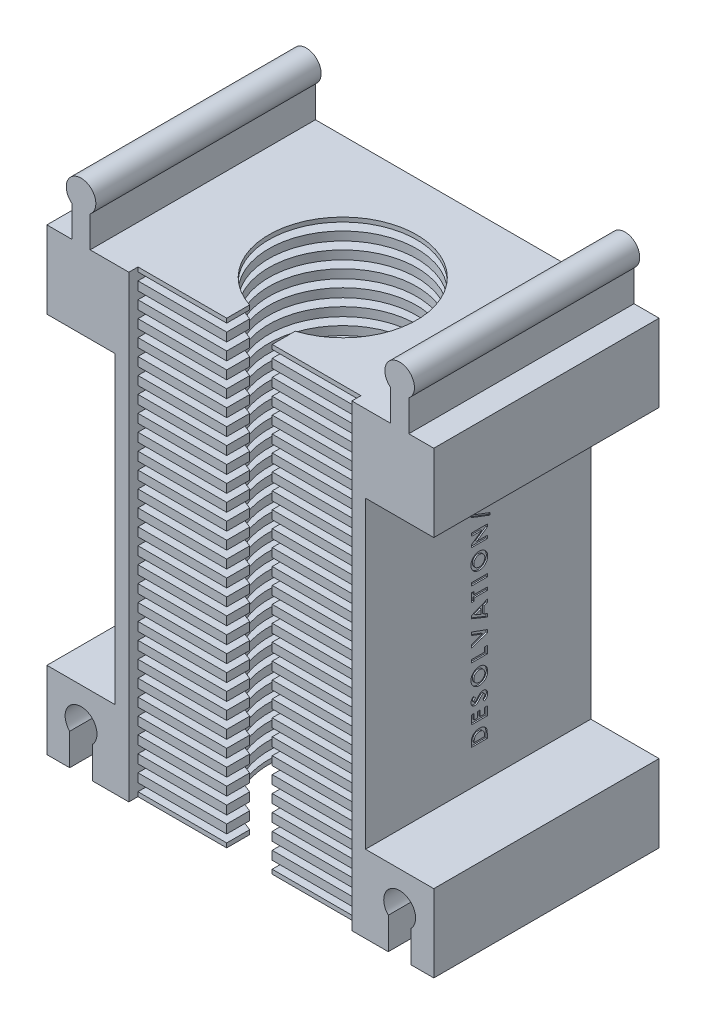
SolidWorks part; units mm, degrees
ref_plane "Plan de face" through (0, 0, 0) normal (0, 0, 1) x (1, 0, 0)
ref_plane "Plan de dessus" through (0, 0, 0) normal (0, 1, 0) x (1, 0, 0)
ref_plane "Plan de droite" through (0, 0, 0) normal (1, 0, 0) x (0, 0, -1)
sketch "Esquisse1" plane through (0, 0, 0) normal (0, 0, 1) x (1, 0, 0)
  line L1 (-20.1477, 24.3067) -> (34.8523, 24.3067)
  line L2 (-20.1477, 24.3067) -> (-20.1477, -82.2433)
  line L3 (-20.1477, -82.2433) -> (34.8523, -82.2433)
  line L4 (34.8523, 24.3067) -> (34.8523, -82.2433)
  dimension "D1" = 55
  dimension "D2" = 106.55
extrude "Boss.-Extru.2" add sketch "Esquisse1" along normal blind 49.5
sketch "Esquisse6" plane through (0, 0, 49.5) normal (0, 0, 1) x (1, 0, 0)
  line L0 (-20.1477, -82.2433) -> (34.8523, -82.2433) construction
  line L1 (-17.1477, 19.5067) -> (31.8523, 19.5067)
  line L2 (-17.1477, 19.5067) -> (-17.1477, -82.2433)
  line L3 (-17.1477, -82.2433) -> (31.8523, -82.2433)
  line L4 (31.8523, 19.5067) -> (31.8523, -82.2433)
  line L5 (-20.1477, 24.3067) -> (-20.1477, -82.2433) construction
  dimension "D1" = 49
  dimension "D2" = 3
  dimension "D3" = 101.75
extrude "Enlèv. mat.-Extru.2" cut sketch "Esquisse6" against normal blind 47
sketch "Esquisse7" plane through (0, 0, 2.5) normal (0, 0, 1) x (1, 0, 0)
  line L0 (31.8523, -82.2433) -> (31.8523, 19.5067) construction
  line L1 (-17.1477, -82.2433) -> (31.8523, -82.2433)
  line L2 (-17.1477, -82.2433) -> (-17.1477, -80.3433)
  line L3 (-17.1477, -80.3433) -> (31.8523, -80.3433)
  line L4 (31.8523, -82.2433) -> (31.8523, -80.3433)
  line L5 (-17.1477, -78.6433) -> (-17.1477, -76.7433)
  line L6 (-17.1477, -78.6433) -> (31.8523, -78.6433)
  line L7 (31.8523, -78.6433) -> (31.8523, -76.7433)
  line L8 (-17.1477, -76.7433) -> (31.8523, -76.7433)
  line L9 (-17.1477, -75.0433) -> (-17.1477, -73.1433)
  line L10 (-17.1477, -75.0433) -> (31.8523, -75.0433)
  line L11 (31.8523, -75.0433) -> (31.8523, -73.1433)
  line L12 (-17.1477, -73.1433) -> (31.8523, -73.1433)
  line L13 (-17.1477, -71.4433) -> (-17.1477, -69.5433)
  line L14 (-17.1477, -71.4433) -> (31.8523, -71.4433)
  line L15 (31.8523, -71.4433) -> (31.8523, -69.5433)
  line L16 (-17.1477, -69.5433) -> (31.8523, -69.5433)
  line L17 (-17.1477, -67.8433) -> (-17.1477, -65.9433)
  line L18 (-17.1477, -67.8433) -> (31.8523, -67.8433)
  line L19 (31.8523, -67.8433) -> (31.8523, -65.9433)
  line L20 (-17.1477, -65.9433) -> (31.8523, -65.9433)
  line L21 (-17.1477, -64.2433) -> (-17.1477, -62.3433)
  line L22 (-17.1477, -64.2433) -> (31.8523, -64.2433)
  line L23 (31.8523, -64.2433) -> (31.8523, -62.3433)
  line L24 (-17.1477, -62.3433) -> (31.8523, -62.3433)
  line L25 (-17.1477, -60.6433) -> (-17.1477, -58.7433)
  line L26 (-17.1477, -60.6433) -> (31.8523, -60.6433)
  line L27 (31.8523, -60.6433) -> (31.8523, -58.7433)
  line L28 (-17.1477, -58.7433) -> (31.8523, -58.7433)
  line L29 (-17.1477, -57.0433) -> (-17.1477, -55.1433)
  line L30 (-17.1477, -57.0433) -> (31.8523, -57.0433)
  line L31 (31.8523, -57.0433) -> (31.8523, -55.1433)
  line L32 (-17.1477, -55.1433) -> (31.8523, -55.1433)
  line L33 (-17.1477, -53.4433) -> (-17.1477, -51.5433)
  line L34 (-17.1477, -53.4433) -> (31.8523, -53.4433)
  line L35 (31.8523, -53.4433) -> (31.8523, -51.5433)
  line L36 (-17.1477, -51.5433) -> (31.8523, -51.5433)
  line L37 (-17.1477, -49.8433) -> (-17.1477, -47.9433)
  line L38 (-17.1477, -49.8433) -> (31.8523, -49.8433)
  line L39 (31.8523, -49.8433) -> (31.8523, -47.9433)
  line L40 (-17.1477, -47.9433) -> (31.8523, -47.9433)
  line L41 (-17.1477, -46.2433) -> (-17.1477, -44.3433)
  line L42 (-17.1477, -46.2433) -> (31.8523, -46.2433)
  line L43 (31.8523, -46.2433) -> (31.8523, -44.3433)
  line L44 (-17.1477, -44.3433) -> (31.8523, -44.3433)
  line L45 (-17.1477, -42.6433) -> (-17.1477, -40.7433)
  line L46 (-17.1477, -42.6433) -> (31.8523, -42.6433)
  line L47 (31.8523, -42.6433) -> (31.8523, -40.7433)
  line L48 (-17.1477, -40.7433) -> (31.8523, -40.7433)
  line L49 (-17.1477, -39.0433) -> (-17.1477, -37.1433)
  line L50 (-17.1477, -39.0433) -> (31.8523, -39.0433)
  line L51 (31.8523, -39.0433) -> (31.8523, -37.1433)
  line L52 (-17.1477, -37.1433) -> (31.8523, -37.1433)
  line L53 (-17.1477, -35.4433) -> (-17.1477, -33.5433)
  line L54 (-17.1477, -35.4433) -> (31.8523, -35.4433)
  line L55 (31.8523, -35.4433) -> (31.8523, -33.5433)
  line L56 (-17.1477, -33.5433) -> (31.8523, -33.5433)
  line L57 (-17.1477, -31.8433) -> (-17.1477, -29.9433)
  line L58 (-17.1477, -31.8433) -> (31.8523, -31.8433)
  line L59 (31.8523, -31.8433) -> (31.8523, -29.9433)
  line L60 (-17.1477, -29.9433) -> (31.8523, -29.9433)
  line L61 (-17.1477, -28.2433) -> (-17.1477, -26.3433)
  line L62 (-17.1477, -28.2433) -> (31.8523, -28.2433)
  line L63 (31.8523, -28.2433) -> (31.8523, -26.3433)
  line L64 (-17.1477, -26.3433) -> (31.8523, -26.3433)
  line L65 (-17.1477, -24.6433) -> (-17.1477, -22.7433)
  line L66 (-17.1477, -24.6433) -> (31.8523, -24.6433)
  line L67 (31.8523, -24.6433) -> (31.8523, -22.7433)
  line L68 (-17.1477, -22.7433) -> (31.8523, -22.7433)
  line L69 (-17.1477, -21.0433) -> (-17.1477, -19.1433)
  line L70 (-17.1477, -21.0433) -> (31.8523, -21.0433)
  line L71 (31.8523, -21.0433) -> (31.8523, -19.1433)
  line L72 (-17.1477, -19.1433) -> (31.8523, -19.1433)
  line L73 (-17.1477, -17.4433) -> (-17.1477, -15.5433)
  line L74 (-17.1477, -17.4433) -> (31.8523, -17.4433)
  line L75 (31.8523, -17.4433) -> (31.8523, -15.5433)
  line L76 (-17.1477, -15.5433) -> (31.8523, -15.5433)
  line L77 (-17.1477, -13.8433) -> (-17.1477, -11.9433)
  line L78 (-17.1477, -13.8433) -> (31.8523, -13.8433)
  line L79 (31.8523, -13.8433) -> (31.8523, -11.9433)
  line L80 (-17.1477, -11.9433) -> (31.8523, -11.9433)
  line L81 (-17.1477, -10.2433) -> (-17.1477, -8.3433)
  line L82 (-17.1477, -10.2433) -> (31.8523, -10.2433)
  line L83 (31.8523, -10.2433) -> (31.8523, -8.3433)
  line L84 (-17.1477, -8.3433) -> (31.8523, -8.3433)
  line L85 (-17.1477, -6.6433) -> (-17.1477, -4.7433)
  line L86 (-17.1477, -6.6433) -> (31.8523, -6.6433)
  line L87 (31.8523, -6.6433) -> (31.8523, -4.7433)
  line L88 (-17.1477, -4.7433) -> (31.8523, -4.7433)
  line L89 (-17.1477, -3.0433) -> (-17.1477, -1.1433)
  line L90 (-17.1477, -3.0433) -> (31.8523, -3.0433)
  line L91 (31.8523, -3.0433) -> (31.8523, -1.1433)
  line L92 (-17.1477, -1.1433) -> (31.8523, -1.1433)
  line L93 (-17.1477, 0.5567) -> (-17.1477, 2.4567)
  line L94 (-17.1477, 0.5567) -> (31.8523, 0.5567)
  line L95 (31.8523, 0.5567) -> (31.8523, 2.4567)
  line L96 (-17.1477, 2.4567) -> (31.8523, 2.4567)
  line L97 (-17.1477, 4.1567) -> (-17.1477, 6.0567)
  line L98 (-17.1477, 4.1567) -> (31.8523, 4.1567)
  line L99 (31.8523, 4.1567) -> (31.8523, 6.0567)
  line L100 (-17.1477, 6.0567) -> (31.8523, 6.0567)
  line L101 (-17.1477, 7.7567) -> (-17.1477, 9.6567)
  line L102 (-17.1477, 7.7567) -> (31.8523, 7.7567)
  line L103 (31.8523, 7.7567) -> (31.8523, 9.6567)
  line L104 (-17.1477, 9.6567) -> (31.8523, 9.6567)
  line L105 (-17.1477, 11.3567) -> (-17.1477, 13.2567)
  line L106 (-17.1477, 11.3567) -> (31.8523, 11.3567)
  line L107 (31.8523, 11.3567) -> (31.8523, 13.2567)
  line L108 (-17.1477, 13.2567) -> (31.8523, 13.2567)
  line L109 (-17.1477, 14.9567) -> (-17.1477, 16.8567)
  line L110 (-17.1477, 14.9567) -> (31.8523, 14.9567)
  line L111 (31.8523, 14.9567) -> (31.8523, 16.8567)
  line L112 (-17.1477, 16.8567) -> (31.8523, 16.8567)
  line L113 (-17.1477, 18.5567) -> (-17.1477, 20.4567)
  line L114 (-17.1477, 18.5567) -> (31.8523, 18.5567)
  line L115 (31.8523, 18.5567) -> (31.8523, 20.4567)
  line L116 (-17.1477, 20.4567) -> (31.8523, 20.4567)
  dimension "D1" = 1.9
  dimension "D2" = 29
extrude "Boss.-Extru.3" add sketch "Esquisse7" along normal blind 45
sketch "Esquisse8" plane through (0, -82.2433, 0) normal (0, -1, 0) x (1, 0, 0)
  line L0 (-17.1477, 47.5) -> (-17.1477, 49.5) construction
  line L1 (-20.1477, 49.5) -> (-20.1477, 0) construction
  circle A0 centre (7.3523, 27) radius 16.25
  point P4 (-17.1477, 48.5)
  dimension "D1" = 32.5
  dimension "D2" = 21.5
  dimension "D3" = 27.5
extrude "Enlèv. mat.-Extru.4" cut sketch "Esquisse8" against normal through all
sketch "Esquisse9" plane through (0, -82.2433, 0) normal (0, -1, 0) x (1, 0, 0)
  line L0 (2.3523, 47.5) -> (2.3523, 42.4616)
  line L1 (-17.1477, 47.5) -> (31.8523, 47.5) construction
  line L2 (12.3523, 47.5) -> (12.3523, 42.4616)
  line L3 (2.3523, 47.5) -> (12.3523, 47.5)
  line L4 (-20.1477, 49.5) -> (-20.1477, 0) construction
  line L5 (2.3523, 42.4616) -> (12.3523, 42.4616)
  circle A0 centre (7.3523, 27) radius 16.25 construction
  dimension "D1" = 10
  dimension "D2" = 22.5
extrude "Enlèv. mat.-Extru.5" cut sketch "Esquisse9" against normal through all
sketch "Esquisse10" plane through (0, -82.2433, 0) normal (0, -1, 0) x (1, 0, 0)
  line L11 (31.8523, 47.5) -> (12.3523, 47.5)
  line L12 (12.3523, 47.5) -> (12.3523, 42.4616)
  line L13 (2.3523, 42.4616) -> (2.3523, 47.5)
  line L14 (2.3523, 47.5) -> (-17.1477, 47.5)
  line L15 (-17.1477, 47.5) -> (-17.1477, 49.5)
  line L16 (-17.1477, 49.5) -> (-20.1477, 49.5)
  line L17 (-20.1477, 49.5) -> (-20.1477, 0)
  line L18 (-20.1477, 0) -> (34.8523, 0)
  line L19 (34.8523, 0) -> (34.8523, 49.5)
  line L20 (34.8523, 49.5) -> (31.8523, 49.5)
  line L21 (31.8523, 49.5) -> (31.8523, 47.5)
  line L22 (31.8523, 47.5) -> (12.3523, 47.5)
  line L23 (12.3523, 47.5) -> (12.3523, 42.4616)
  line L24 (2.3523, 42.4616) -> (2.3523, 47.5)
  line L25 (2.3523, 47.5) -> (-17.1477, 47.5)
  line L26 (-17.1477, 47.5) -> (-17.1477, 49.5)
  line L27 (-17.1477, 49.5) -> (-20.1477, 49.5)
  line L28 (-20.1477, 49.5) -> (-20.1477, 0)
  line L29 (-20.1477, 0) -> (34.8523, 0)
  line L30 (34.8523, 0) -> (34.8523, 49.5)
  line L31 (34.8523, 49.5) -> (31.8523, 49.5)
  line L32 (31.8523, 49.5) -> (31.8523, 47.5)
  arc A1 (2.3523, 42.4616) -> (12.3523, 42.4616) centre (7.3523, 27) ccw
  arc A2 (2.3523, 42.4616) -> (12.3523, 42.4616) centre (7.3523, 27) ccw
  dimension "D1" = 0
sketch "Esquisse11" plane through (0, 24.3067, 0) normal (0, 1, 0) x (1, 0, 0)
  line L4 (34.8523, 0) -> (-20.1477, 0)
  line L5 (-20.1477, 0) -> (-20.1477, -49.5)
  line L6 (-20.1477, -49.5) -> (34.8523, -49.5)
  line L7 (34.8523, -49.5) -> (34.8523, 0)
  line L8 (34.8523, 0) -> (-20.1477, 0)
  line L9 (-20.1477, 0) -> (-20.1477, -49.5)
  line L10 (-20.1477, -49.5) -> (34.8523, -49.5)
  line L11 (34.8523, -49.5) -> (34.8523, 0)
  dimension "D1" = 0
extrude "Enlèv. mat.-Extru.6" cut sketch "Esquisse11" against normal blind 4.8
sketch "Esquisse14" plane through (0, 0, 49.5) normal (0, 0, 1) x (1, 0, 0)
  line L1 (34.8523, -82.2433) -> (49.8523, -82.2433)
  line L2 (34.8523, -82.2433) -> (34.8523, -64.2933)
  line L3 (34.8523, -64.2933) -> (49.8523, -64.2933)
  line L4 (49.8523, -82.2433) -> (49.8523, -64.2933)
  dimension "D1" = 15
  dimension "D2" = 17.95
extrude "Boss.-Extru.5" add sketch "Esquisse14" against normal up to surface (49.5 mm away) up to face at (7.3523, -31.3683, 0)
sketch "Esquisse15" plane through (0, 0, 49.5) normal (0, 0, 1) x (1, 0, 0)
  line L1 (-20.1477, -82.2433) -> (-35.1477, -82.2433)
  line L2 (-20.1477, -82.2433) -> (-20.1477, -64.2933)
  line L3 (-20.1477, -64.2933) -> (-35.1477, -64.2933)
  line L4 (-35.1477, -82.2433) -> (-35.1477, -64.2933)
  dimension "D1" = 17.95
  dimension "D2" = 15
extrude "Boss.-Extru.6" add sketch "Esquisse15" against normal up to surface (49.5 mm away) up to face at (21.5189, -42.3433, 0)
sketch "Esquisse16" plane through (0, 0, 49.5) normal (0, 0, 1) x (1, 0, 0)
  line L1 (34.8523, 19.5067) -> (49.8523, 19.5067)
  line L2 (34.8523, 19.5067) -> (34.8523, 2.5067)
  line L3 (34.8523, 2.5067) -> (49.8523, 2.5067)
  line L4 (49.8523, 19.5067) -> (49.8523, 2.5067)
  dimension "D1" = 17
  dimension "D2" = 15
extrude "Boss.-Extru.7" add sketch "Esquisse16" against normal up to surface (49.5 mm away) up to face at (7.3523, -47.8308, 0)
sketch "Esquisse17" plane through (0, 0, 49.5) normal (0, 0, 1) x (1, 0, 0)
  line L1 (-20.1477, 19.5067) -> (-35.1477, 19.5067)
  line L2 (-20.1477, 19.5067) -> (-20.1477, 2.5067)
  line L3 (-20.1477, 2.5067) -> (-35.1477, 2.5067)
  line L4 (-35.1477, 19.5067) -> (-35.1477, 2.5067)
  dimension "D1" = 15
  dimension "D2" = 17
extrude "Boss.-Extru.8" add sketch "Esquisse17" against normal up to surface (49.5 mm away) up to face at (15.8523, -37.7633, 0)
sketch "Esquisse18" plane through (0, 0, 49.5) normal (0, 0, 1) x (1, 0, 0)
  line L0 (44.8523, -74.3433) -> (44.8523, -82.2433)
  line L2 (44.8523, -82.2433) -> (39.8523, -82.2433)
  line L3 (39.8523, -82.2433) -> (39.8523, -74.3433)
  line L4 (7.3523, -82.2443) -> (7.3523, -64.1566) construction
  line L5 (49.8523, -82.2433) -> (49.8523, -64.2933) construction
  line L7 (-30.1477, -82.2433) -> (-25.1477, -82.2433)
  line L8 (-30.1477, -74.3433) -> (-30.1477, -82.2433)
  line L9 (-25.1477, -82.2433) -> (-25.1477, -74.3433)
  line L15 (31.8523, -82.2433) -> (49.8523, -82.2433) construction
  arc A0 (44.8523, -74.3433) -> (39.8523, -74.3433) centre (42.3523, -71.8938) ccw
  arc A1 (-30.1477, -74.3433) -> (-25.1477, -74.3433) centre (-27.6477, -71.8938) cw
  dimension "D5" = 3.5
  dimension "D1" = 5
  dimension "D2" = 5
  dimension "D3" = 7.9
  dimension "D4" = 7.9
extrude "Enlèv. mat.-Extru.8" cut sketch "Esquisse18" against normal through all
sketch "Esquisse20" plane through (0, 0, 49.5) normal (0, 0, 1) x (1, 0, 0)
  line L0 (-29.6477, 26.3467) -> (-29.6477, 19.5067)
  line L1 (-35.1477, 19.5067) -> (-17.1477, 19.5067) construction
  line L2 (-29.6477, 19.5067) -> (-25.6477, 19.5067)
  line L3 (-25.6477, 19.5067) -> (-25.6477, 26.3467)
  line L4 (-35.1477, 19.5067) -> (-35.1477, 2.5067) construction
  line L5 (7.3523, 19.5067) -> (7.3523, 35.4205) construction
  line L6 (23.6023, 19.5067) -> (-8.8977, 19.5067) construction
  line L7 (40.3523, 19.5067) -> (40.3523, 26.3467)
  line L8 (44.3523, 19.5067) -> (40.3523, 19.5067)
  line L9 (44.3523, 26.3467) -> (44.3523, 19.5067)
  arc A0 (-25.6477, 26.3467) -> (-29.6477, 26.3467) centre (-27.6477, 28.9084) ccw
  arc A1 (40.3523, 26.3467) -> (44.3523, 26.3467) centre (42.3523, 28.9084) cw
  dimension "D3" = 3.25
  dimension "D1" = 5.5
  dimension "D2" = 4
  dimension "D4" = 6.84
  dimension "D5" = 6.84
extrude "Boss.-Extru.9" add sketch "Esquisse20" against normal up to surface (49.5 mm away) up to face at (7.3523, -49.3534, 0)
sketch "Esquisse21" plane through (34.8523, 0, 0) normal (1, 0, 0) x (0, 0, -1)
  line L0 (-22.75, -64.2933) -> (-22.75, 2.5067) construction
  line L1 (0, -64.2933) -> (-49.5, -64.2933) construction
  line L2 (0, 2.5067) -> (-49.5, 2.5067) construction
  line L3 (-49.5, -64.2933) -> (-49.5, 2.5067) construction
  text T0 "<b>DESOLVATION/28</b>" font "Century Gothic" height 3.5
  dimension "D1" = 26.75
extrude "Enlèv. mat.-Extru.9" cut sketch "Esquisse21" against normal blind 0.3
extrude "Enlèv. mat.-Extru.10" cut sketch "Esquisse10" against normal blind 0.95
sketch "Esquisse22" plane through (0, -82.2433, 0) normal (0, -1, 0) x (1, 0, 0)
  line L0 (49.8523, 49.5) -> (44.8523, 49.5) construction
  line L1 (44.8523, 49.5) -> (44.8523, 0) construction
  line L2 (44.8523, 0) -> (49.8523, 0) construction
  line L3 (49.8523, 0) -> (49.8523, 49.5) construction
  line L4 (39.8523, 49.5) -> (34.8523, 49.5) construction
  line L5 (34.8523, 49.5) -> (34.8523, 0) construction
  line L6 (34.8523, 0) -> (39.8523, 0) construction
  line L7 (39.8523, 0) -> (39.8523, 49.5) construction
  line L8 (-35.1477, 0) -> (-30.1477, 0) construction
  line L9 (-30.1477, 0) -> (-30.1477, 49.5) construction
  line L10 (-30.1477, 49.5) -> (-35.1477, 49.5) construction
  line L11 (-35.1477, 49.5) -> (-35.1477, 0) construction
  line L12 (-25.1477, 0) -> (-20.1477, 0) construction
  line L13 (-20.1477, 0) -> (-20.1477, 49.5) construction
  line L14 (-20.1477, 49.5) -> (-25.1477, 49.5) construction
  line L15 (-25.1477, 49.5) -> (-25.1477, 0) construction
  line L16 (49.8523, 49.5) -> (44.8523, 49.5)
  line L17 (44.8523, 49.5) -> (44.8523, 0)
  line L18 (44.8523, 0) -> (49.8523, 0)
  line L19 (49.8523, 0) -> (49.8523, 49.5)
  line L20 (39.8523, 49.5) -> (34.8523, 49.5)
  line L21 (34.8523, 49.5) -> (34.8523, 0)
  line L22 (34.8523, 0) -> (39.8523, 0)
  line L23 (39.8523, 0) -> (39.8523, 49.5)
  line L24 (-35.1477, 0) -> (-30.1477, 0)
  line L25 (-30.1477, 0) -> (-30.1477, 49.5)
  line L26 (-30.1477, 49.5) -> (-35.1477, 49.5)
  line L27 (-35.1477, 49.5) -> (-35.1477, 0)
  line L28 (-25.1477, 0) -> (-20.1477, 0)
  line L29 (-20.1477, 0) -> (-20.1477, 49.5)
  line L30 (-20.1477, 49.5) -> (-25.1477, 49.5)
  line L31 (-25.1477, 49.5) -> (-25.1477, 0)
extrude "Enlèv. mat.-Extru.11" cut sketch "Esquisse22" against normal up to surface (0.95 mm away) up to face at (7.3523, -81.2933, 36.7676)
